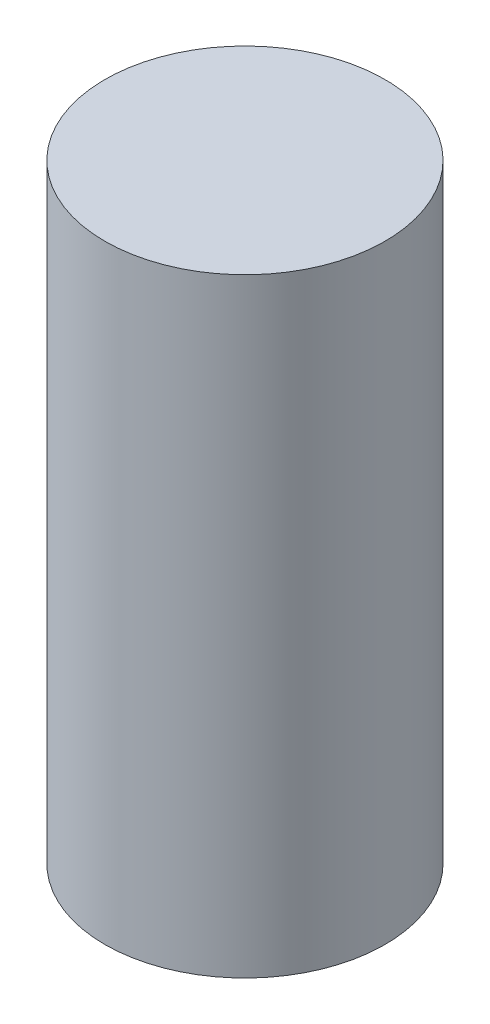
SolidWorks part; units mm, degrees
ref_plane "Plano frontal" through (0, 0, 0) normal (0, 0, 1) x (1, 0, 0)
ref_plane "Plano superior" through (0, 0, 0) normal (0, 1, 0) x (1, 0, 0)
ref_plane "Plano direito" through (0, 0, 0) normal (1, 0, 0) x (0, 0, -1)
sketch "Esboço1" plane through (0, 0, 0) normal (0, 1, 0) x (1, 0, 0)
  circle A0 centre (0, 0) radius 8.05
  dimension "D1" = 16.1
extrude "Ressalto-extrusão1" add sketch "Esboço1" along normal blind 35
